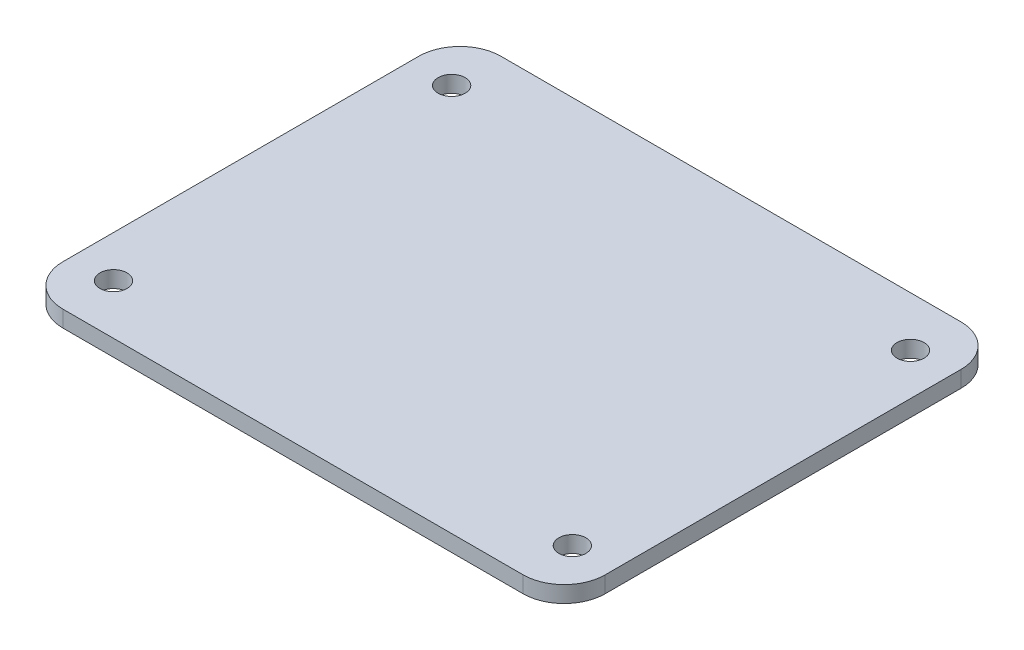
SolidWorks part; units mm, degrees
ref_plane "Plan de face" through (0, 0, 0) normal (0, 0, 1) x (1, 0, 0)
ref_plane "Plan de dessus" through (0, 0, 0) normal (0, 1, 0) x (1, 0, 0)
ref_plane "Plan de droite" through (0, 0, 0) normal (1, 0, 0) x (0, 0, -1)
sketch "Esquisse1" plane through (0, 0, 0) normal (0, 1, 0) x (1, 0, 0)
  line L1 (-33.02, 26.67) -> (33.02, 26.67)
  line L2 (-33.02, 26.67) -> (-33.02, -26.67)
  line L3 (-33.02, -26.67) -> (33.02, -26.67)
  line L4 (33.02, 26.67) -> (33.02, -26.67)
  line L5 (-33.02, 26.67) -> (33.02, -26.67) construction
  line L6 (-33.02, -26.67) -> (33.02, 26.67) construction
  line L7 (-27.94, 20.59) -> (27.94, 20.59) construction
  line L8 (-27.94, 20.59) -> (-27.94, -20.59) construction
  line L9 (-27.94, -20.59) -> (27.94, -20.59) construction
  line L10 (27.94, 20.59) -> (27.94, -20.59) construction
  line L11 (-27.94, 20.59) -> (27.94, -20.59) construction
  line L12 (-27.94, -20.59) -> (27.94, 20.59) construction
  circle A0 centre (-27.94, 20.59) radius 1.65
  circle A1 centre (27.94, 20.59) radius 1.65
  circle A2 centre (27.94, -20.59) radius 1.65
  circle A3 centre (-27.94, -20.59) radius 1.65
  point P0 (0, 0)
  point P6 (0, 0)
  dimension "D5" = 3.3
  dimension "D6" = 3.3
  dimension "D7" = 3.3
  dimension "D8" = 3.3
  dimension "D1" = 66.04
  dimension "D2" = 53.34
  dimension "D3" = 41.18
  dimension "D4" = 55.88
extrude "Boss.-Extru.1" add sketch "Esquisse1" along normal blind 2
fillet "Congé1" radius 5 4 edges at (-33.02, 1, -26.67) (33.02, 1, -26.67) (33.02, 1, 26.67) (-33.02, 1, 26.67)
